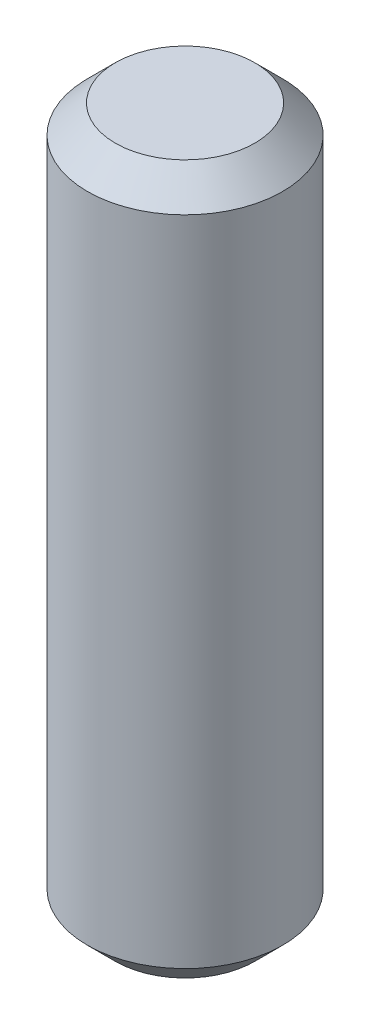
SolidWorks part; units mm, degrees
material "Cast Stainless Steel"
ref_plane "Front Plane" through (0, 0, 0) normal (0, 0, 1) x (1, 0, 0)
ref_plane "Top Plane" through (0, 0, 0) normal (0, 1, 0) x (1, 0, 0)
ref_plane "Right Plane" through (0, 0, 0) normal (1, 0, 0) x (0, 0, -1)
sketch "Sketch1" plane through (0, 0, 0) normal (0, 1, 0) x (1, 0, 0)
  circle A0 centre (0, 0) radius 1.75
  dimension "D1" = 3.5
extrude "Boss-Extrude1" add sketch "Sketch1" along normal blind 12.7
chamfer "Chamfer1" distance 0.5 angle 45 2 edges at (0, 0, 1.75) (0, 12.7, 1.75)
